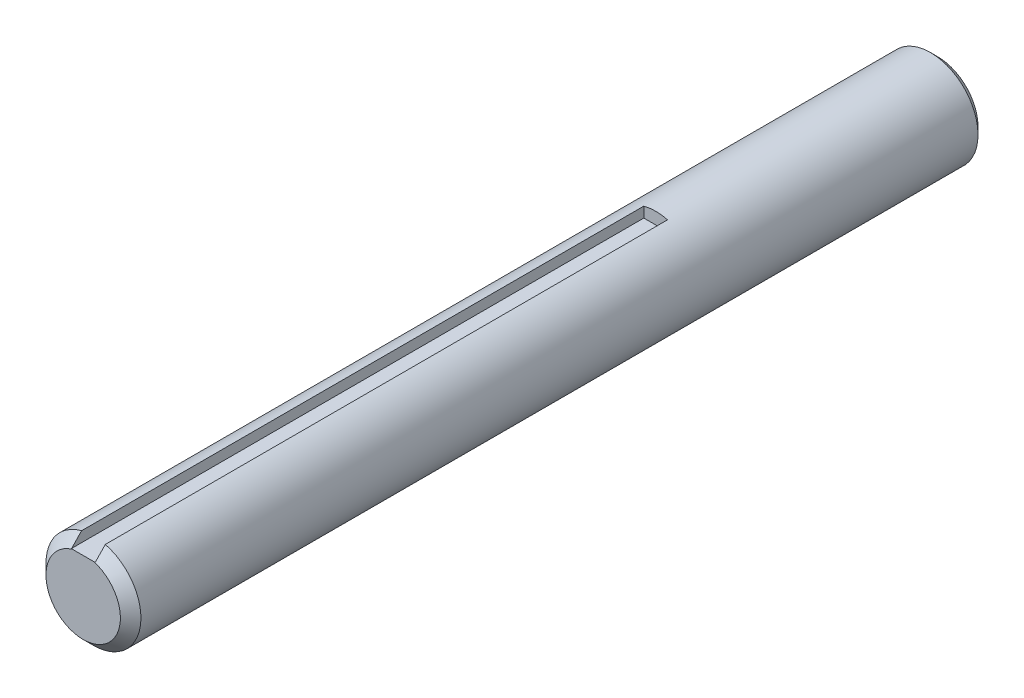
SolidWorks part; units mm, degrees
ref_plane "Front" through (0, 0, 0) normal (0, 0, 1) x (1, 0, 0)
ref_plane "Top" through (0, 0, 0) normal (0, 1, 0) x (1, 0, 0)
ref_plane "Right" through (0, 0, 0) normal (1, 0, 0) x (0, 0, -1)
sketch "Sketch1" plane through (0, 0, 0) normal (0, 0, 1) x (1, 0, 0)
  circle A0 centre (0, 0) radius 6.35
  dimension "dia" = 12.7
extrude "Extrude1" add sketch "Sketch1" along normal mid plane 152.4
sketch "Sketch2" plane through (0, 0, 0) normal (1, 0, 0) x (0, 0, -1)
  point P0 (-76.2, 6.35)
  point P1 (76.2, 6.35)
  point P2 (76.2, -6.35)
chamfer "Chamfer1" distance 0.9525 angle 45 2 edges at (6.35, 0, -76.2) (6.35, 0, 76.2)
sketch "Sketch3" plane through (0, 0, 0) normal (0, 0, 1) x (1, 0, 0)
  line L1 (-1.5875, 6.35) -> (1.5875, 6.35)
  line L2 (-1.5875, 6.35) -> (-1.5875, 4.7625)
  line L3 (-1.5875, 4.7625) -> (1.5875, 4.7625)
  line L4 (1.5875, 6.35) -> (1.5875, 4.7625)
  dimension "key wd" = 3.175
  dimension "key dp" = 1.5875
extrude "Extrude2" cut sketch "Sketch3" against normal blind 38.481 and the other way through all
ref_plane "Plane1" through (0, 0, 38.1) normal (0, 0, 1) x (1, 0, 0)
other "SurfaceCut1"
chamfer "Chamfer2" distance 1.3735 angle 45 1 edges at (0, -6.35, 38.1)
equation "\"D1@Chamfer1\" = \"dia@Sketch1\" * .075"
